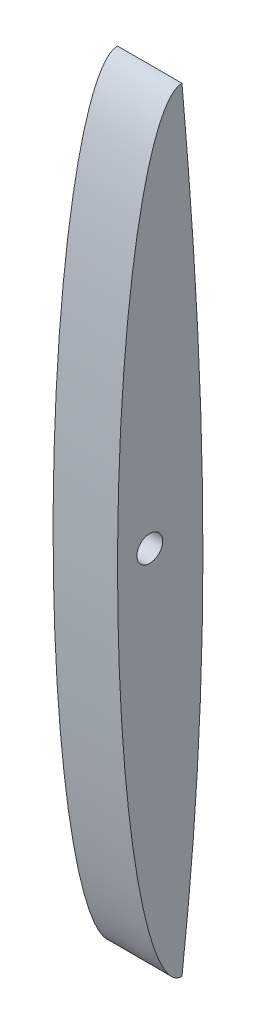
SolidWorks part; units mm, degrees
ref_plane "Front Plane" through (0, 0, 0) normal (0, 0, 1) x (1, 0, 0)
ref_plane "Top Plane" through (0, 0, 0) normal (0, 1, 0) x (1, 0, 0)
ref_plane "Right Plane" through (0, 0, 0) normal (1, 0, 0) x (0, 0, -1)
sketch "Sketch1" plane through (0, 0, 0) normal (1, 0, 0) x (0, 0, -1)
  line L0 (0, 0) -> (0, -60) construction
  line L1 (-5, -30) -> (0, -30) construction
  circle A0 centre (-2.5, -30) radius 1
  ellipse E0 centre (0, -30) end of major axis (0, -60) minor radius 5 (0, 0) -> (0, -60) ccw
  spline S0 degree 3 poles (0, 0) (0.0002, -0.0017) (0.0008, -0.0096) (0.002, -0.0231) (0.0035, -0.0401) (0.0049, -0.0559) (0.0061, -0.0705) (0.0074, -0.0844) (0.0085, -0.0975) (0.0096, -0.11) (0.0106, -0.122) (0.0116, -0.1334) (0.0125, -0.1439) (0.0134, -0.1535) (0.0141, -0.1621) (0.0148, -0.1698) (0.0154, -0.1766) (0.0159, -0.1825) (0.0163, -0.1873) (0.0166, -0.1911) (0.0169, -0.194) (0.0171, -0.1962) (0.0172, -0.1982) (0.0174, -0.2) (0.0176, -0.202) (0.0178, -0.2041) (0.0181, -0.208) (0.0186, -0.214) (0.0193, -0.2222) (0.0201, -0.2309) (0.0209, -0.2402) (0.0218, -0.2502) (0.0228, -0.2619) (0.0239, -0.2752) (0.0252, -0.2903) (0.0267, -0.3066) (0.0282, -0.3241) (0.0298, -0.3427) (0.0315, -0.3624) (0.0333, -0.3831) (0.0351, -0.4046) (0.037, -0.4265) (0.039, -0.4485) (0.0409, -0.4708) (0.0437, -0.5036) (0.0475, -0.5473) (0.0521, -0.6004) (0.0566, -0.6528) (0.0611, -0.7045) (0.0656, -0.7571) (0.0702, -0.8106) (0.0748, -0.8647) (0.0795, -0.9194) (0.0843, -0.9745) (0.0891, -1.0306) (0.094, -1.0879) (0.099, -1.1464) (0.1041, -1.2062) (0.1093, -1.2669) (0.1146, -1.3285) (0.1199, -1.3906) (0.1252, -1.4533) (0.1306, -1.5164) (0.136, -1.5804) (0.1416, -1.6458) (0.1472, -1.7124) (0.153, -1.7805) (0.1588, -1.8493) (0.1646, -1.9187) (0.1705, -1.9885) (0.1765, -2.0588) (0.1834, -2.1411) (0.1913, -2.2355) (0.2003, -2.3422) (0.2093, -2.4499) (0.2183, -2.5585) (0.2275, -2.668) (0.2365, -2.7763) (0.2453, -2.8834) (0.2541, -2.9893) (0.2629, -3.0959) (0.2718, -3.2034) (0.2807, -3.3118) (0.2896, -3.4209) (0.2987, -3.5309) (0.3077, -3.6418) (0.3168, -3.7534) (0.3246, -3.8489) (0.331, -3.928) (0.336, -3.9901) (0.341, -4.0518) (0.3456, -4.1082) (0.3497, -4.1595) (0.3534, -4.2056) (0.3571, -4.251) (0.3609, -4.2982) (0.3648, -4.3472) (0.3689, -4.3979) (0.3729, -4.4475) (0.3767, -4.4961) (0.3806, -4.5438) (0.3843, -4.5904) (0.3878, -4.6348) (0.3912, -4.677) (0.3944, -4.717) (0.3975, -4.7563) (0.4006, -4.7946) (0.4035, -4.8322) (0.406, -4.8627) (0.4078, -4.8863) (0.4092, -4.9033) (0.4105, -4.9195) (0.4117, -4.9349) (0.4128, -4.9494) (0.4139, -4.9629) (0.4149, -4.9758) (0.4159, -4.9881) (0.4168, -4.9997) (0.4177, -5.0101) (0.4184, -5.0194) (0.419, -5.0272) (0.4195, -5.0336) (0.4199, -5.0387) (0.4202, -5.043) (0.4205, -5.0467) (0.4208, -5.0502) (0.4212, -5.0544) (0.4215, -5.0594) (0.422, -5.0655) (0.4226, -5.0723) (0.4232, -5.0801) (0.4239, -5.0889) (0.4247, -5.0989) (0.4255, -5.1097) (0.4264, -5.1214) (0.4274, -5.1341) (0.4285, -5.1473) (0.4296, -5.1611) (0.4307, -5.1755) (0.4319, -5.1907) (0.4332, -5.2067) (0.4345, -5.2241) (0.436, -5.2432) (0.4377, -5.2638) (0.4394, -5.2855) (0.4411, -5.3081) (0.443, -5.3318) (0.4449, -5.3564) (0.4469, -5.382) (0.4491, -5.41) (0.4515, -5.4402) (0.454, -5.4724) (0.4566, -5.5048) (0.4591, -5.5373) (0.4616, -5.5697) (0.4641, -5.602) (0.4704, -5.6826) (0.4806, -5.8132) (0.4945, -5.9932) (0.5085, -6.1742) (0.5223, -6.3542) (0.5359, -6.5331) (0.5485, -6.6984) (0.56, -6.8503) (0.5704, -6.989) (0.5808, -7.1275) (0.5912, -7.266) (0.6079, -7.4895) (0.6307, -7.7982) (0.6507, -8.0715) (0.6618, -8.2243) (0.6642, -8.2567) (0.6665, -8.2891) (0.6689, -8.3214) (0.6712, -8.3535) (0.6736, -8.3868) (0.6761, -8.421) (0.6786, -8.4559) (0.681, -8.4897) (0.6834, -8.5226) (0.6857, -8.5545) (0.6879, -8.5855) (0.6901, -8.6152) (0.6921, -8.6438) (0.6941, -8.6712) (0.696, -8.6974) (0.6977, -8.7224) (0.6994, -8.7461) (0.7011, -8.7687) (0.7026, -8.7901) (0.704, -8.8103) (0.7052, -8.8273) (0.7062, -8.8413) (0.707, -8.8525) (0.7078, -8.8628) (0.7084, -8.8722) (0.709, -8.8804) (0.7095, -8.8873) (0.7099, -8.893) (0.7103, -8.8975) (0.7105, -8.9014) (0.7108, -8.9052) (0.7111, -8.9093) (0.7114, -8.9137) (0.7118, -8.9192) (0.7123, -8.926) (0.7129, -8.934) (0.7135, -8.9429) (0.7142, -8.953) (0.715, -8.9644) (0.7159, -8.9773) (0.7169, -8.9911) (0.718, -9.006) (0.7191, -9.0218) (0.7203, -9.0386) (0.7215, -9.0564) (0.7229, -9.0755) (0.7243, -9.0959) (0.7259, -9.1178) (0.7275, -9.1407) (0.7292, -9.1647) (0.731, -9.1898) (0.7328, -9.2151) (0.7346, -9.2406) (0.7364, -9.2662) (0.7382, -9.2927) (0.7402, -9.32) (0.7421, -9.3483) (0.7442, -9.3769) (0.7462, -9.4057) (0.7482, -9.4348) (0.7503, -9.4647) (0.7525, -9.4954) (0.7547, -9.5269) (0.7569, -9.5592) (0.7592, -9.5923) (0.7616, -9.6262) (0.764, -9.6608) (0.7688, -9.7302) (0.7771, -9.8501) (0.7889, -10.0202) (0.8016, -10.2057) (0.8145, -10.3947) (0.8275, -10.5871) (0.8407, -10.783) (0.8537, -10.9779) (0.8665, -11.1718) (0.8774, -11.3365) (0.8863, -11.4723) (0.8917, -11.555) (0.8955, -11.613) (0.8977, -11.6466) (0.8998, -11.68) (0.902, -11.7132) (0.9043, -11.7488) (0.9067, -11.7866) (0.9093, -11.8264) (0.9118, -11.8651) (0.9142, -11.9029) (0.9166, -11.9396) (0.9189, -11.9754) (0.9211, -12.0101) (0.9233, -12.0438) (0.9254, -12.0765) (0.9274, -12.1082) (0.9294, -12.1388) (0.9313, -12.1685) (0.9331, -12.1971) (0.9348, -12.224) (0.9364, -12.2492) (0.9379, -12.2728) (0.9393, -12.2955) (0.9407, -12.3174) (0.9421, -12.3384) (0.9432, -12.3567) (0.9442, -12.3724) (0.945, -12.3854) (0.9458, -12.3976) (0.9465, -12.4089) (0.9472, -12.4192) (0.9478, -12.4285) (0.9483, -12.4369) (0.9487, -12.4443) (0.9492, -12.4514) (0.9496, -12.4586) (0.9502, -12.468) (0.951, -12.48) (0.9519, -12.4946) (0.9529, -12.51) (0.9539, -12.5261) (0.955, -12.5438) (0.9562, -12.5631) (0.9575, -12.5839) (0.9589, -12.6058) (0.9603, -12.6287) (0.9618, -12.6525) (0.9634, -12.6773) (0.965, -12.7032) (0.9666, -12.7295) (0.9683, -12.7563) (0.97, -12.7836) (0.9718, -12.8118) (0.9736, -12.8409) (0.9754, -12.8708) (0.9773, -12.9011) (0.9792, -12.9316) (0.9811, -12.9623) (0.983, -12.9938) (0.985, -13.0261) (0.9871, -13.0592) (0.9892, -13.0931) (0.9913, -13.1278) (0.9935, -13.1632) (0.9957, -13.1995) (0.998, -13.2363) (1.0002, -13.2737) (1.0026, -13.3117) (1.0049, -13.3503) (1.0077, -13.3964) (1.011, -13.4502) (1.0147, -13.5118) (1.0185, -13.5746) (1.0223, -13.6385) (1.0263, -13.7036) (1.0301, -13.7685) (1.034, -13.8332) (1.0379, -13.8978) (1.0417, -13.9633) (1.0457, -14.0299) (1.0496, -14.0966) (1.0536, -14.1635) (1.0575, -14.2304) (1.0615, -14.2983) (1.0655, -14.3672) (1.0696, -14.437) (1.0736, -14.5064) (1.0776, -14.5753) (1.0815, -14.6437) (1.0855, -14.713) (1.0895, -14.7831) (1.0936, -14.8541) (1.0977, -14.9259) (1.1018, -14.9986) (1.1059, -15.0721) (1.1101, -15.1464) (1.1134, -15.2055) (1.1159, -15.2491) (1.1175, -15.277) (1.119, -15.305) (1.1206, -15.3329) (1.1221, -15.3604) (1.1237, -15.3886) (1.1253, -15.4174) (1.1269, -15.4466) (1.1285, -15.4746) (1.1299, -15.5008) (1.1313, -15.5253) (1.1325, -15.5481) (1.1337, -15.5699) (1.1349, -15.5906) (1.1359, -15.6104) (1.137, -15.6291) (1.1379, -15.6463) (1.1388, -15.6622) (1.1396, -15.6767) (1.1403, -15.6903) (1.141, -15.7031) (1.1417, -15.715) (1.1423, -15.7261) (1.1429, -15.7364) (1.1434, -15.7457) (1.1438, -15.7543) (1.1443, -15.7619) (1.1446, -15.7688) (1.1449, -15.7744) (1.1452, -15.7789) (1.1454, -15.7825) (1.1455, -15.7856) (1.1457, -15.7885) (1.1459, -15.7917) (1.1461, -15.7956) (1.1463, -15.8002) (1.1466, -15.8055) (1.147, -15.8115) (1.1473, -15.818) (1.1477, -15.8248) (1.1481, -15.8319) (1.1485, -15.8392) (1.149, -15.8497) (1.1498, -15.8635) (1.1507, -15.881) (1.1518, -15.9) (1.1529, -15.9205) (1.1541, -15.9426) (1.1553, -15.9657) (1.1567, -15.9901) (1.1581, -16.017) (1.1597, -16.0461) (1.1614, -16.0773) (1.163, -16.1088) (1.1648, -16.1406) (1.1665, -16.1725) (1.1682, -16.2048) (1.1704, -16.2464) (1.1731, -16.2976) (1.1764, -16.3585) (1.1797, -16.4218) (1.1832, -16.4875) (1.1868, -16.5555) (1.1904, -16.6245) (1.194, -16.6944) (1.1977, -16.7652) (1.2014, -16.837) (1.2052, -16.9098) (1.209, -16.9835) (1.2128, -17.0583) (1.2167, -17.1337) (1.2205, -17.2097) (1.2244, -17.2863) (1.2283, -17.3639) (1.2321, -17.4406) (1.2359, -17.5163) (1.2396, -17.5908) (1.2434, -17.6663) (1.2471, -17.7427) (1.2509, -17.8199) (1.2547, -17.8981) (1.2587, -17.9797) (1.2628, -18.0651) (1.2671, -18.154) (1.2714, -18.2441) (1.2758, -18.3352) (1.2793, -18.4087) (1.2819, -18.4643) (1.2836, -18.5017) (1.2854, -18.539) (1.2871, -18.5758) (1.2888, -18.6117) (1.2904, -18.6465) (1.2919, -18.6792) (1.2934, -18.7098) (1.2947, -18.7386) (1.296, -18.7663) (1.2972, -18.7931) (1.2984, -18.8188) (1.2995, -18.8436) (1.3006, -18.8674) (1.3017, -18.8902) (1.3027, -18.912) (1.3036, -18.9328) (1.3045, -18.9526) (1.3054, -18.9711) (1.3062, -18.9883) (1.3069, -19.0042) (1.3076, -19.0193) (1.3082, -19.0335) (1.3089, -19.0474) (1.3095, -19.061) (1.3101, -19.0741) (1.3106, -19.086) (1.3111, -19.0968) (1.3115, -19.1064) (1.3119, -19.1148) (1.3122, -19.1214) (1.3124, -19.1265) (1.3126, -19.1302) (1.3128, -19.1336) (1.3129, -19.1373) (1.3131, -19.1415) (1.3134, -19.1465) (1.3136, -19.1523) (1.3139, -19.1595) (1.3143, -19.1682) (1.3148, -19.1786) (1.3153, -19.19) (1.3159, -19.2023) (1.3165, -19.2157) (1.3171, -19.2297) (1.3178, -19.2443) (1.3184, -19.2596) (1.3192, -19.2757) (1.3199, -19.2927) (1.3207, -19.311) (1.3216, -19.3305) (1.3225, -19.3514) (1.3235, -19.3733) (1.3245, -19.3961) (1.3256, -19.4199) (1.3272, -19.4558) (1.3293, -19.5038) (1.3321, -19.5675) (1.3351, -19.6357) (1.3383, -19.7085) (1.3416, -19.7853) (1.3451, -19.8662) (1.3487, -19.9511) (1.3524, -20.0371) (1.3561, -20.1242) (1.3598, -20.2124) (1.3635, -20.3016) (1.3672, -20.3893) (1.3707, -20.4755) (1.3742, -20.5601) (1.3777, -20.6454) (1.3812, -20.7313) (1.3846, -20.8173) (1.391, -20.9767) (1.4002, -21.2094) (1.4119, -21.5152) (1.4231, -21.8142) (1.4307, -22.0218) (1.4349, -22.1382) (1.436, -22.1695) (1.4371, -22.2002) (1.4381, -22.2281) (1.439, -22.2528) (1.4398, -22.2747) (1.4406, -22.2958) (1.4413, -22.3171) (1.4421, -22.3385) (1.4428, -22.3598) (1.4435, -22.3802) (1.4442, -22.3996) (1.4449, -22.4181) (1.4455, -22.4356) (1.4461, -22.4522) (1.4466, -22.4681) (1.4471, -22.4832) (1.4476, -22.4975) (1.4481, -22.5107) (1.4485, -22.523) (1.4489, -22.5341) (1.4493, -22.5445) (1.4496, -22.5539) (1.4499, -22.5624) (1.4502, -22.5697) (1.4503, -22.5753) (1.4505, -22.5797) (1.4506, -22.5835) (1.4508, -22.5879) (1.451, -22.5928) (1.4512, -22.5988) (1.4514, -22.606) (1.4517, -22.6145) (1.452, -22.6237) (1.4524, -22.6336) (1.4527, -22.6442) (1.4531, -22.6555) (1.4536, -22.6682) (1.454, -22.6824) (1.4546, -22.6982) (1.4552, -22.7149) (1.4558, -22.7325) (1.4564, -22.7511) (1.457, -22.7702) (1.4577, -22.7897) (1.4584, -22.8098) (1.4591, -22.8307) (1.4598, -22.8524) (1.4606, -22.8762) (1.4615, -22.9021) (1.4624, -22.9302) (1.4634, -22.9595) (1.4644, -22.9899) (1.4654, -23.019) (1.4663, -23.0467) (1.4672, -23.0729) (1.4681, -23.0997) (1.469, -23.1271) (1.4702, -23.1661) (1.4719, -23.2161) (1.4738, -23.2767) (1.4758, -23.3365) (1.4778, -23.3992) (1.4799, -23.4645) (1.482, -23.5324) (1.4841, -23.5991) (1.4861, -23.6647) (1.4881, -23.729) (1.4901, -23.7921) (1.492, -23.8541) (1.4938, -23.9148) (1.4956, -23.9744) (1.4974, -24.0328) (1.4991, -24.0899) (1.5006, -24.142) (1.502, -24.1892) (1.5032, -24.2316) (1.5044, -24.2735) (1.5057, -24.3153) (1.5069, -24.3575) (1.5082, -24.4044) (1.5097, -24.456) (1.5113, -24.5125) (1.5129, -24.5701) (1.5146, -24.6287) (1.5162, -24.6883) (1.5179, -24.7478) (1.5195, -24.8071) (1.5211, -24.8662) (1.5227, -24.9262) (1.5243, -24.9872) (1.526, -25.049) (1.5276, -25.1118) (1.5293, -25.1755) (1.531, -25.2402) (1.5326, -25.3058) (1.5341, -25.3623) (1.5353, -25.4094) (1.5362, -25.4464) (1.5371, -25.4826) (1.538, -25.5181) (1.5389, -25.5526) (1.5397, -25.5864) (1.5405, -25.6209) (1.5414, -25.6562) (1.5423, -25.692) (1.5431, -25.7268) (1.5439, -25.7604) (1.5447, -25.7929) (1.5454, -25.8243) (1.5461, -25.8538) (1.5468, -25.8815) (1.5474, -25.9073) (1.548, -25.9323) (1.5486, -25.9563) (1.5491, -25.9794) (1.5495, -25.9984) (1.5499, -26.0137) (1.5502, -26.0254) (1.5504, -26.0367) (1.5507, -26.0474) (1.5509, -26.0573) (1.5511, -26.0668) (1.5513, -26.0759) (1.5515, -26.0844) (1.5517, -26.0918) (1.5518, -26.0976) (1.5519, -26.1022) (1.552, -26.106) (1.5521, -26.1097) (1.5522, -26.1138) (1.5523, -26.119) (1.5525, -26.1254) (1.5526, -26.1331) (1.5528, -26.1419) (1.5531, -26.1519) (1.5533, -26.1631) (1.5536, -26.1754) (1.5539, -26.1886) (1.5542, -26.2028) (1.5545, -26.2181) (1.5549, -26.2343) (1.5553, -26.2518) (1.5557, -26.2707) (1.5562, -26.291) (1.5566, -26.3123) (1.5571, -26.3348) (1.5577, -26.3583) (1.5582, -26.3817) (1.5587, -26.4049) (1.5592, -26.4277) (1.5597, -26.4512) (1.5602, -26.475) (1.5607, -26.499) (1.5612, -26.523) (1.5625, -26.5831) (1.5647, -26.6864) (1.5677, -26.833) (1.5708, -26.987) (1.5738, -27.1417) (1.5767, -27.2971) (1.5796, -27.4532) (1.5824, -27.61) (1.5851, -27.7674) (1.588, -27.9426) (1.5911, -28.135) (1.5942, -28.3442) (1.5973, -28.5526) (1.6001, -28.7601) (1.6028, -28.9667) (1.6046, -29.1136) (1.6056, -29.2011) (1.6059, -29.2294) (1.6063, -29.2575) (1.6066, -29.2851) (1.6069, -29.3118) (1.6072, -29.3371) (1.6074, -29.3609) (1.6077, -29.3834) (1.6079, -29.405) (1.6081, -29.4257) (1.6084, -29.4456) (1.6086, -29.4645) (1.6088, -29.4826) (1.6089, -29.4998) (1.6091, -29.5162) (1.6093, -29.5316) (1.6094, -29.546) (1.6096, -29.5595) (1.6097, -29.5721) (1.6098, -29.5839) (1.6099, -29.595) (1.61, -29.6053) (1.6101, -29.6146) (1.6102, -29.6231) (1.6103, -29.6307) (1.6104, -29.6374) (1.6104, -29.6434) (1.6105, -29.6487) (1.6105, -29.6536) (1.6106, -29.6585) (1.6106, -29.6639) (1.6107, -29.6701) (1.6108, -29.6772) (1.6108, -29.6853) (1.6109, -29.6942) (1.611, -29.7041) (1.6111, -29.7152) (1.6112, -29.7272) (1.6114, -29.7403) (1.6115, -29.7543) (1.6117, -29.7693) (1.6118, -29.7849) (1.612, -29.8011) (1.6121, -29.8178) (1.6123, -29.8355) (1.6125, -29.8539) (1.6126, -29.8733) (1.6128, -29.8935) (1.613, -29.9145) (1.6132, -29.9364) (1.6134, -29.9592) (1.6136, -29.9826) (1.6138, -30.0068) (1.614, -30.0316) (1.6143, -30.0573) (1.6145, -30.0866) (1.6148, -30.1193) (1.6151, -30.1552) (1.6154, -30.1913) (1.6157, -30.2274) (1.6159, -30.2635) (1.6162, -30.2996) (1.6169, -30.3898) (1.6184, -30.602) (1.6204, -30.9361) (1.6217, -31.2291) (1.6223, -31.4129) (1.6226, -31.4878) (1.6228, -31.5627) (1.623, -31.6376) (1.6232, -31.7124) (1.6233, -31.7816) (1.6234, -31.8447) (1.6235, -31.9017) (1.6236, -31.9578) (1.6236, -32.0129) (1.6237, -32.0672) (1.6237, -32.1207) (1.6238, -32.1732) (1.6238, -32.2249) (1.6238, -32.2756) (1.6238, -32.3255) (1.6238, -32.3745) (1.6237, -32.4218) (1.6237, -32.4672) (1.6237, -32.511) (1.6236, -32.554) (1.6236, -32.5962) (1.6235, -32.6356) (1.6235, -32.6722) (1.6234, -32.7061) (1.6234, -32.7349) (1.6233, -32.7589) (1.6233, -32.778) (1.6233, -32.7964) (1.6232, -32.8133) (1.6232, -32.8285) (1.6232, -32.8422) (1.6231, -32.8549) (1.6231, -32.8667) (1.6231, -32.8775) (1.6231, -32.8874) (1.623, -32.8964) (1.623, -32.9042) (1.623, -32.9109) (1.623, -32.9165) (1.623, -32.9214) (1.623, -32.9255) (1.623, -32.9292) (1.6229, -32.9331) (1.6229, -32.9377) (1.6229, -32.9433) (1.6229, -32.9499) (1.6229, -32.9576) (1.6229, -32.9663) (1.6228, -32.9761) (1.6228, -32.9867) (1.6228, -32.9981) (1.6227, -33.0099) (1.6227, -33.0253) (1.6226, -33.0445) (1.6226, -33.0679) (1.6225, -33.0922) (1.6224, -33.1176) (1.6223, -33.1438) (1.6222, -33.1708) (1.6221, -33.1987) (1.622, -33.2275) (1.6219, -33.2575) (1.6218, -33.2887) (1.6217, -33.3211) (1.6215, -33.3546) (1.6214, -33.389) (1.6212, -33.4245) (1.621, -33.461) (1.6209, -33.4984) (1.6207, -33.5369) (1.6205, -33.5763) (1.6203, -33.6165) (1.6201, -33.6571) (1.6198, -33.7105) (1.6194, -33.7764) (1.6189, -33.8518) (1.6185, -33.9236) (1.618, -33.9918) (1.6176, -34.0594) (1.617, -34.1305) (1.6165, -34.2049) (1.6159, -34.2826) (1.6153, -34.3594) (1.6146, -34.4351) (1.614, -34.5098) (1.6133, -34.5813) (1.6127, -34.6496) (1.6121, -34.7148) (1.6115, -34.7793) (1.6108, -34.8433) (1.6102, -34.9073) (1.6092, -35.0008) (1.6078, -35.124) (1.606, -35.2774) (1.6041, -35.4319) (1.6027, -35.5429) (1.6018, -35.6101) (1.6015, -35.6331) (1.6012, -35.6558) (1.6009, -35.678) (1.6006, -35.6993) (1.6003, -35.7192) (1.6001, -35.7378) (1.5998, -35.7552) (1.5996, -35.7716) (1.5994, -35.7872) (1.5992, -35.8026) (1.599, -35.8177) (1.5988, -35.8324) (1.5986, -35.846) (1.5984, -35.8583) (1.5982, -35.8695) (1.5981, -35.8795) (1.598, -35.8874) (1.5979, -35.8936) (1.5978, -35.8986) (1.5977, -35.9041) (1.5976, -35.9104) (1.5975, -35.9175) (1.5974, -35.9253) (1.5973, -35.9337) (1.5972, -35.9425) (1.597, -35.9545) (1.5968, -35.9696) (1.5965, -35.9883) (1.5962, -36.008) (1.5959, -36.0288) (1.5956, -36.049) (1.5953, -36.0684) (1.595, -36.0868) (1.5947, -36.1055) (1.5944, -36.1245) (1.594, -36.1521) (1.5934, -36.1886) (1.5927, -36.2344) (1.592, -36.2812) (1.5912, -36.3293) (1.5905, -36.3726) (1.5899, -36.4111) (1.5893, -36.4445) (1.5887, -36.4783) (1.5882, -36.5126) (1.5876, -36.5473) (1.587, -36.5829) (1.5863, -36.6188) (1.5857, -36.6548) (1.5851, -36.6899) (1.5845, -36.7239) (1.5839, -36.7569) (1.5833, -36.7886) (1.5828, -36.8193) (1.5822, -36.849) (1.5817, -36.8779) (1.5811, -36.9061) (1.5806, -36.9335) (1.5801, -36.9599) (1.5797, -36.9854) (1.5792, -37.0099) (1.5787, -37.0334) (1.5783, -37.0544) (1.578, -37.0735) (1.5776, -37.0912) (1.5773, -37.1095) (1.5769, -37.1285) (1.5765, -37.1481) (1.5761, -37.1682) (1.5757, -37.1889) (1.5753, -37.2103) (1.5748, -37.2339) (1.5743, -37.2597) (1.5737, -37.2878) (1.5732, -37.3169) (1.5725, -37.3469) (1.5719, -37.3779) (1.5712, -37.4109) (1.5705, -37.4459) (1.5697, -37.483) (1.5689, -37.5213) (1.5681, -37.5607) (1.5672, -37.6012) (1.5663, -37.6429) (1.5654, -37.6845) (1.5645, -37.7259) (1.5636, -37.7671) (1.5626, -37.8093) (1.5617, -37.8525) (1.5607, -37.8966) (1.5598, -37.9348) (1.5591, -37.9671) (1.5585, -37.993) (1.5579, -38.0193) (1.5572, -38.0458) (1.5566, -38.0723) (1.556, -38.1) (1.5553, -38.1285) (1.5546, -38.1576) (1.5539, -38.186) (1.5533, -38.2136) (1.5526, -38.2405) (1.552, -38.2666) (1.5514, -38.2919) (1.5508, -38.3162) (1.5502, -38.3396) (1.5496, -38.3621) (1.5491, -38.3834) (1.5486, -38.4035) (1.5481, -38.4225) (1.5477, -38.4406) (1.5472, -38.4579) (1.5468, -38.4744) (1.5464, -38.4908) (1.546, -38.5072) (1.5456, -38.5233) (1.5452, -38.5383) (1.5449, -38.5516) (1.5446, -38.5634) (1.5443, -38.5738) (1.5441, -38.5832) (1.5439, -38.5917) (1.5437, -38.5993) (1.5435, -38.6059) (1.5433, -38.6116) (1.5432, -38.6159) (1.5432, -38.619) (1.5431, -38.6213) (1.543, -38.6237) (1.543, -38.6266) (1.5429, -38.6302) (1.5427, -38.6347) (1.5426, -38.6401) (1.5424, -38.6464) (1.5423, -38.6536) (1.5421, -38.6612) (1.5419, -38.6692) (1.5416, -38.6791) (1.5413, -38.6911) (1.5409, -38.7053) (1.5405, -38.7203) (1.5401, -38.7362) (1.5397, -38.753) (1.5392, -38.7711) (1.5387, -38.7906) (1.5381, -38.8115) (1.5375, -38.8334) (1.5369, -38.8566) (1.5362, -38.8813) (1.5356, -38.9072) (1.5344, -38.948) (1.5329, -39.003) (1.5311, -39.0693) (1.5294, -39.1322) (1.5277, -39.1917) (1.526, -39.2504) (1.5245, -39.303) (1.5232, -39.3497) (1.522, -39.3907) (1.5208, -39.4311) (1.5197, -39.4712) (1.5185, -39.5107) (1.5173, -39.5499) (1.5161, -39.5905) (1.5148, -39.6332) (1.5135, -39.6781) (1.5121, -39.7242) (1.5107, -39.7714) (1.5092, -39.8196) (1.5076, -39.869) (1.5061, -39.9194) (1.5044, -39.971) (1.5028, -40.0236) (1.5011, -40.077) (1.4993, -40.1311) (1.4976, -40.186) (1.4958, -40.242) (1.4939, -40.2971) (1.4922, -40.3515) (1.4904, -40.405) (1.4886, -40.4593) (1.487, -40.5056) (1.4857, -40.5436) (1.4847, -40.5731) (1.4837, -40.6025) (1.4827, -40.6314) (1.4817, -40.6595) (1.4808, -40.6868) (1.4799, -40.7131) (1.479, -40.7386) (1.4782, -40.7631) (1.4773, -40.7868) (1.4765, -40.8096) (1.4758, -40.8312) (1.4751, -40.8514) (1.4744, -40.8705) (1.4737, -40.8888) (1.4731, -40.9063) (1.4725, -40.9233) (1.4719, -40.9398) (1.4714, -40.9558) (1.4708, -40.9709) (1.4703, -40.9851) (1.4698, -40.9984) (1.4694, -41.0106) (1.469, -41.0218) (1.4686, -41.0319) (1.4683, -41.0413) (1.468, -41.0498) (1.4677, -41.0572) (1.4675, -41.0635) (1.4673, -41.069) (1.4671, -41.0745) (1.4669, -41.0803) (1.4666, -41.0865) (1.4664, -41.0924) (1.4662, -41.0981) (1.466, -41.1038) (1.4658, -41.1104) (1.4655, -41.118) (1.4652, -41.1265) (1.4648, -41.136) (1.4645, -41.1468) (1.464, -41.1588) (1.4635, -41.172) (1.463, -41.1864) (1.4624, -41.2019) (1.4618, -41.2184) (1.4612, -41.2347) (1.4606, -41.2506) (1.4601, -41.2659) (1.4595, -41.2818) (1.4589, -41.2979) (1.4583, -41.314) (1.4572, -41.3438) (1.4556, -41.3869) (1.4534, -41.4432) (1.4513, -41.5001) (1.4491, -41.5575) (1.4469, -41.6154) (1.4447, -41.6725) (1.4425, -41.7288) (1.4402, -41.7864) (1.4379, -41.8452) (1.4355, -41.9052) (1.4332, -41.9641) (1.4308, -42.022) (1.4285, -42.0789) (1.4263, -42.1347) (1.424, -42.1896) (1.4218, -42.244) (1.4195, -42.2981) (1.4173, -42.3517) (1.4151, -42.4043) (1.4129, -42.4557) (1.4108, -42.506) (1.4087, -42.5553) (1.4067, -42.6022) (1.4048, -42.6467) (1.403, -42.689) (1.4012, -42.7303) (1.3994, -42.7707) (1.3977, -42.8102) (1.3961, -42.847) (1.3946, -42.881) (1.3932, -42.9123) (1.3919, -42.9427) (1.3906, -42.9722) (1.3893, -43.0009) (1.3881, -43.0286) (1.3868, -43.0564) (1.3856, -43.084) (1.3843, -43.1115) (1.3831, -43.1379) (1.382, -43.1632) (1.3809, -43.1868) (1.3799, -43.2087) (1.379, -43.2289) (1.3781, -43.2483) (1.3773, -43.2668) (1.3765, -43.2844) (1.3757, -43.3011) (1.375, -43.3175) (1.3742, -43.3333) (1.3735, -43.3486) (1.3729, -43.3629) (1.3723, -43.3761) (1.3717, -43.3882) (1.3712, -43.3993) (1.3707, -43.4093) (1.3703, -43.4182) (1.37, -43.4261) (1.3697, -43.4321) (1.3695, -43.4364) (1.3693, -43.4398) (1.3691, -43.4438) (1.3689, -43.4483) (1.3687, -43.4533) (1.3684, -43.4587) (1.3682, -43.4647) (1.3678, -43.4723) (1.3674, -43.4817) (1.3668, -43.4929) (1.3663, -43.5054) (1.3656, -43.5189) (1.3649, -43.5336) (1.3642, -43.5492) (1.3634, -43.5655) (1.3626, -43.5825) (1.3618, -43.6005) (1.3609, -43.6196) (1.36, -43.6385) (1.3591, -43.6571) (1.3583, -43.6751) (1.3574, -43.6934) (1.3565, -43.7117) (1.3557, -43.7299) (1.3544, -43.7562) (1.3528, -43.7905) (1.3503, -43.8414) (1.3475, -43.9003) (1.3442, -43.9672) (1.341, -44.0331) (1.3378, -44.0982) (1.3349, -44.1563) (1.3324, -44.2077) (1.3301, -44.2524) (1.3279, -44.2968) (1.3257, -44.3412) (1.3234, -44.3862) (1.3211, -44.4323) (1.3187, -44.478) (1.3164, -44.5235) (1.3141, -44.5685) (1.3117, -44.6145) (1.3093, -44.6614) (1.3068, -44.7092) (1.3042, -44.76) (1.3014, -44.8138) (1.2984, -44.8707) (1.2953, -44.9288) (1.2921, -44.988) (1.2889, -45.048) (1.2857, -45.1087) (1.2824, -45.1702) (1.279, -45.2329) (1.2762, -45.283) (1.2742, -45.3204) (1.2729, -45.3443) (1.2716, -45.3678) (1.2703, -45.3906) (1.2691, -45.4126) (1.2679, -45.4351) (1.2666, -45.4579) (1.2654, -45.481) (1.2641, -45.503) (1.263, -45.5241) (1.2618, -45.5443) (1.2608, -45.5635) (1.2598, -45.5816) (1.2588, -45.5987) (1.2579, -45.6147) (1.2571, -45.6295) (1.2563, -45.6433) (1.2556, -45.656) (1.2549, -45.6675) (1.2544, -45.678) (1.2538, -45.6874) (1.2534, -45.6957) (1.253, -45.7028) (1.2526, -45.7089) (1.2523, -45.7139) (1.2521, -45.7176) (1.252, -45.7202) (1.2519, -45.7224) (1.2517, -45.7251) (1.2515, -45.7285) (1.2513, -45.7327) (1.251, -45.7376) (1.2507, -45.7431) (1.2503, -45.749) (1.25, -45.7555) (1.2496, -45.7622) (1.2491, -45.7715) (1.2484, -45.7835) (1.2475, -45.7985) (1.2466, -45.8145) (1.2457, -45.8315) (1.2446, -45.8494) (1.2436, -45.868) (1.2425, -45.8871) (1.2414, -45.9067) (1.2402, -45.9272) (1.239, -45.9486) (1.2376, -45.9719) (1.2362, -45.9973) (1.2346, -46.0247) (1.2329, -46.0532) (1.2313, -46.0807) (1.2298, -46.1069) (1.2284, -46.1316) (1.2269, -46.1569) (1.2247, -46.194) (1.2219, -46.2425) (1.2184, -46.3021) (1.2148, -46.3623) (1.2112, -46.4232) (1.2075, -46.4846) (1.2039, -46.5452) (1.2003, -46.6049) (1.1967, -46.6638) (1.1932, -46.7218) (1.1897, -46.779) (1.1863, -46.8354) (1.1829, -46.8909) (1.1795, -46.9453) (1.1762, -46.9986) (1.1729, -47.0511) (1.1697, -47.1035) (1.1657, -47.1672) (1.1609, -47.2425) (1.1554, -47.3293) (1.1498, -47.417) (1.1444, -47.5019) (1.1391, -47.584) (1.1353, -47.6426) (1.1328, -47.6809) (1.1317, -47.6986) (1.1305, -47.7159) (1.1294, -47.7325) (1.1284, -47.7485) (1.1274, -47.7639) (1.1264, -47.7798) (1.1253, -47.7961) (1.1242, -47.8127) (1.1232, -47.8282) (1.1222, -47.8426) (1.1213, -47.856) (1.1205, -47.8682) (1.1198, -47.8791) (1.1192, -47.8888) (1.1186, -47.8971) (1.1181, -47.9046) (1.1177, -47.9114) (1.1173, -47.9177) (1.1169, -47.9234) (1.1165, -47.9287) (1.1162, -47.9342) (1.1158, -47.9402) (1.1153, -47.9468) (1.1149, -47.9541) (1.1143, -47.9627) (1.1136, -47.9726) (1.1129, -47.984) (1.1121, -47.9962) (1.1112, -48.0099) (1.1101, -48.0249) (1.109, -48.0415) (1.1079, -48.0591) (1.1066, -48.0779) (1.1053, -48.0978) (1.1039, -48.1183) (1.1025, -48.1396) (1.101, -48.1614) (1.0995, -48.1843) (1.0979, -48.2081) (1.0962, -48.2329) (1.0944, -48.2588) (1.0926, -48.2856) (1.0907, -48.3135) (1.0888, -48.3423) (1.0848, -48.4014) (1.0787, -48.4905) (1.0705, -48.6091) (1.0623, -48.7273) (1.0541, -48.8445) (1.0457, -48.9637) (1.0371, -49.0849) (1.0282, -49.208) (1.0194, -49.3299) (1.0107, -49.4507) (1.0019, -49.5703) (0.9953, -49.6593) (0.991, -49.7179) (0.9889, -49.7462) (0.9868, -49.7739) (0.9848, -49.8008) (0.9829, -49.827) (0.9809, -49.854) (0.9788, -49.8815) (0.9767, -49.9096) (0.9747, -49.9367) (0.9727, -49.963) (0.9708, -49.9884) (0.9689, -50.013) (0.9672, -50.0365) (0.9655, -50.059) (0.9638, -50.0804) (0.9623, -50.1008) (0.9608, -50.1201) (0.9594, -50.1383) (0.9581, -50.1555) (0.9569, -50.1717) (0.9558, -50.1868) (0.9547, -50.2008) (0.9537, -50.2138) (0.9528, -50.2257) (0.9519, -50.2367) (0.9512, -50.2458) (0.9507, -50.2534) (0.9502, -50.2599) (0.9496, -50.2668) (0.9491, -50.2745) (0.9484, -50.2828) (0.9477, -50.2925) (0.9468, -50.3036) (0.9459, -50.3162) (0.9448, -50.3297) (0.9438, -50.3435) (0.9427, -50.3573) (0.9416, -50.3711) (0.9405, -50.3853) (0.9394, -50.3997) (0.9383, -50.4142) (0.9367, -50.4354) (0.9345, -50.4634) (0.9311, -50.5077) (0.9269, -50.5619) (0.9219, -50.6255) (0.9169, -50.6895) (0.9118, -50.7538) (0.9067, -50.8191) (0.9014, -50.8855) (0.8961, -50.953) (0.8916, -51.0085) (0.8882, -51.052) (0.8857, -51.0833) (0.8831, -51.1153) (0.8805, -51.1481) (0.8777, -51.1817) (0.8748, -51.2182) (0.8716, -51.2577) (0.8682, -51.3003) (0.8646, -51.344) (0.8609, -51.389) (0.8572, -51.4354) (0.8532, -51.4832) (0.8492, -51.5322) (0.8451, -51.5822) (0.8409, -51.633) (0.8367, -51.6847) (0.8323, -51.7371) (0.8279, -51.7906) (0.8233, -51.8452) (0.8187, -51.9008) (0.8139, -51.9576) (0.809, -52.0154) (0.8047, -52.0668) (0.8009, -52.1116) (0.7977, -52.1491) (0.7946, -52.1863) (0.7915, -52.2225) (0.7885, -52.257) (0.7857, -52.2899) (0.7831, -52.3211) (0.7805, -52.3516) (0.7779, -52.3811) (0.7755, -52.4097) (0.7731, -52.4372) (0.7708, -52.4638) (0.7686, -52.4895) (0.7664, -52.5145) (0.7643, -52.5386) (0.7623, -52.5619) (0.7604, -52.5844) (0.7587, -52.6035) (0.7573, -52.6194) (0.7562, -52.6323) (0.7551, -52.6447) (0.7541, -52.6564) (0.7532, -52.6675) (0.7523, -52.6776) (0.7515, -52.6869) (0.7508, -52.695) (0.7501, -52.702) (0.7496, -52.7079) (0.7492, -52.7124) (0.749, -52.7156) (0.7487, -52.7181) (0.7485, -52.7206) (0.7483, -52.7234) (0.748, -52.7266) (0.7476, -52.731) (0.7471, -52.7367) (0.7465, -52.7441) (0.7457, -52.7524) (0.7449, -52.7617) (0.744, -52.772) (0.743, -52.7833) (0.742, -52.7956) (0.7408, -52.8089) (0.7395, -52.8231) (0.7382, -52.8383) (0.7368, -52.8545) (0.7354, -52.8703) (0.734, -52.8857) (0.7328, -52.9003) (0.7314, -52.9152) (0.7301, -52.9302) (0.7253, -52.9847) (0.7174, -53.0742) (0.7063, -53.1987) (0.6945, -53.33) (0.6816, -53.4727) (0.6704, -53.5957) (0.662, -53.6877) (0.6564, -53.749) (0.6507, -53.8107) (0.6446, -53.8772) (0.638, -53.9484) (0.631, -54.0245) (0.6238, -54.1015) (0.6165, -54.1794) (0.6091, -54.2583) (0.6014, -54.34) (0.5934, -54.4245) (0.5851, -54.5119) (0.5767, -54.6003) (0.5685, -54.6862) (0.5605, -54.7694) (0.5543, -54.8334) (0.5497, -54.8815) (0.5466, -54.9131) (0.5436, -54.9444) (0.5403, -54.9779) (0.5369, -55.0137) (0.5332, -55.0514) (0.5296, -55.0881) (0.5261, -55.1238) (0.5228, -55.1583) (0.5195, -55.1918) (0.5164, -55.2234) (0.5135, -55.2531) (0.5107, -55.281) (0.5081, -55.3081) (0.5055, -55.3342) (0.503, -55.3594) (0.5006, -55.3842) (0.4981, -55.4087) (0.4958, -55.4327) (0.4935, -55.4556) (0.4916, -55.4743) (0.4902, -55.4889) (0.4891, -55.4997) (0.4881, -55.5102) (0.4871, -55.5203) (0.4861, -55.5296) (0.4853, -55.5381) (0.4845, -55.5457) (0.4839, -55.5525) (0.4833, -55.5583) (0.4828, -55.5634) (0.4824, -55.5675) (0.482, -55.5712) (0.4816, -55.5752) (0.4811, -55.5799) (0.4806, -55.5855) (0.4799, -55.5921) (0.4792, -55.5997) (0.4783, -55.6082) (0.4774, -55.6177) (0.4763, -55.628) (0.4752, -55.6393) (0.474, -55.6514) (0.4727, -55.6643) (0.4713, -55.6781) (0.4699, -55.6929) (0.4683, -55.7088) (0.4666, -55.7255) (0.4649, -55.7426) (0.4631, -55.76) (0.4614, -55.7775) (0.4596, -55.7952) (0.4567, -55.8236) (0.4528, -55.8629) (0.4477, -55.9135) (0.4424, -55.9652) (0.4371, -56.018) (0.4316, -56.072) (0.4261, -56.1259) (0.4206, -56.1799) (0.4151, -56.2337) (0.4095, -56.2886) (0.4037, -56.3445) (0.3979, -56.4013) (0.3919, -56.4592) (0.3858, -56.518) (0.3796, -56.5778) (0.3733, -56.6385) (0.3669, -56.6999) (0.3605, -56.7617) (0.354, -56.8236) (0.3475, -56.8855) (0.3313, -57.0387) (0.3054, -57.2833) (0.2693, -57.6193) (0.2318, -57.9633) (0.2051, -58.206) (0.1894, -58.3471) (0.1859, -58.3787) (0.1824, -58.4101) (0.1789, -58.441) (0.1756, -58.4708) (0.1724, -58.4997) (0.1693, -58.5275) (0.1662, -58.5546) (0.1633, -58.5809) (0.1604, -58.6066) (0.1576, -58.6316) (0.1549, -58.6557) (0.1523, -58.679) (0.1497, -58.7013) (0.1473, -58.7226) (0.145, -58.743) (0.1428, -58.7625) (0.1406, -58.7824) (0.1383, -58.8024) (0.1361, -58.8224) (0.1339, -58.8413) (0.1319, -58.859) (0.13, -58.8756) (0.1285, -58.8892) (0.1273, -58.9002) (0.1263, -58.9087) (0.1254, -58.9168) (0.1245, -58.9244) (0.1237, -58.9315) (0.1229, -58.9382) (0.1223, -58.9441) (0.1217, -58.9492) (0.1212, -58.9532) (0.1209, -58.9559) (0.1207, -58.9578) (0.1205, -58.9593) (0.1203, -58.9613) (0.12, -58.9644) (0.1195, -58.9686) (0.1189, -58.9742) (0.1181, -58.9809) (0.1172, -58.9885) (0.1162, -58.9971) (0.1152, -59.0066) (0.114, -59.0172) (0.1126, -59.0287) (0.1112, -59.0413) (0.1097, -59.0549) (0.108, -59.0691) (0.1064, -59.0837) (0.1046, -59.0989) (0.1028, -59.1149) (0.1009, -59.1318) (0.0988, -59.1495) (0.0967, -59.1685) (0.0943, -59.1888) (0.0919, -59.2105) (0.0893, -59.2331) (0.0865, -59.2567) (0.0837, -59.2813) (0.0808, -59.3063) (0.0779, -59.3318) (0.0749, -59.3577) (0.0718, -59.3844) (0.0687, -59.4119) (0.0654, -59.4404) (0.062, -59.4696) (0.0585, -59.4998) (0.0549, -59.5308) (0.0512, -59.5627) (0.0474, -59.5952) (0.0435, -59.6284) (0.0396, -59.6622) (0.0356, -59.6969) (0.0314, -59.7326) (0.0271, -59.7694) (0.0227, -59.8072) (0.0181, -59.846) (0.0135, -59.8855) (0.0088, -59.9257) (0.0042, -59.964) (0.0013, -59.9887) (0, -60) knots 0 0 0 0 0.000087 0.000391 0.000679 0.000937 0.001181 0.001413 0.001631 0.001835 0.002041 0.002231 0.002406 0.002565 0.002709 0.002838 0.002951 0.003049 0.003132 0.003192 0.00324 0.003276 0.003306 0.003337 0.00337 0.003404 0.00344 0.003565 0.003707 0.003848 0.004002 0.00417 0.004351 0.004585 0.004838 0.005109 0.0054 0.00571 0.006039 0.006387 0.006749 0.007114 0.007482 0.007853 0.008228 0.009124 0.010039 0.010886 0.011749 0.012626 0.013519 0.014426 0.015333 0.016253 0.017189 0.018139 0.019121 0.020118 0.021131 0.022158 0.023201 0.02424 0.025293 0.026361 0.027443 0.028563 0.029697 0.030847 0.032005 0.033171 0.034343 0.035523 0.037287 0.039068 0.040863 0.042675 0.044502 0.046344 0.048096 0.049861 0.05164 0.053433 0.05524 0.057061 0.058896 0.060744 0.062607 0.064483 0.06552 0.066562 0.067594 0.068606 0.069387 0.070156 0.070913 0.071658 0.072519 0.073364 0.074192 0.075004 0.075798 0.076575 0.077336 0.078018 0.078687 0.079341 0.079981 0.080606 0.081218 0.081506 0.081791 0.082064 0.082321 0.082562 0.082788 0.082997 0.083209 0.083402 0.083576 0.083731 0.083867 0.083965 0.08405 0.084122 0.084181 0.084236 0.0843 0.084388 0.084488 0.084602 0.084728 0.084879 0.085045 0.085225 0.085421 0.085632 0.085857 0.086084 0.086324 0.086577 0.086843 0.087123 0.087451 0.087795 0.088156 0.088534 0.088928 0.089339 0.089766 0.09021 0.090738 0.091279 0.09182 0.092361 0.092901 0.09344 0.093979 0.096934 0.09997 0.102988 0.105989 0.108973 0.11194 0.114258 0.116568 0.118877 0.121187 0.123498 0.130059 0.136626 0.137166 0.137705 0.138245 0.138785 0.139323 0.139848 0.14045 0.141033 0.141596 0.142141 0.142677 0.143193 0.143689 0.144165 0.144622 0.145058 0.145475 0.145871 0.146247 0.146604 0.14694 0.147257 0.147454 0.147642 0.147816 0.147972 0.148109 0.148229 0.148317 0.148393 0.148454 0.148515 0.148582 0.148656 0.148736 0.148858 0.148993 0.149141 0.149301 0.149499 0.149713 0.149943 0.150191 0.150454 0.150735 0.151031 0.151344 0.15169 0.152054 0.152436 0.152837 0.153255 0.153691 0.154103 0.154529 0.154971 0.155427 0.155898 0.156384 0.156856 0.157341 0.15784 0.158352 0.158877 0.159415 0.159966 0.160531 0.161109 0.161696 0.164002 0.167108 0.1702 0.173277 0.176559 0.179823 0.183071 0.186303 0.189518 0.191308 0.193092 0.193651 0.194211 0.194769 0.195324 0.195869 0.196549 0.197212 0.197859 0.198488 0.1991 0.199696 0.200274 0.200836 0.201381 0.201909 0.20242 0.202914 0.203391 0.203851 0.204258 0.204651 0.205029 0.205394 0.205744 0.20608 0.206311 0.206528 0.206731 0.206919 0.207092 0.20725 0.207385 0.207507 0.207622 0.207741 0.207864 0.208094 0.208338 0.208594 0.208864 0.209147 0.209478 0.209826 0.21019 0.210571 0.210968 0.211382 0.211812 0.212259 0.212699 0.213154 0.213623 0.214108 0.214607 0.215121 0.21562 0.216132 0.216657 0.217195 0.217746 0.218311 0.218889 0.21948 0.220084 0.220702 0.221321 0.221953 0.222598 0.223252 0.224259 0.225286 0.226332 0.227396 0.228481 0.229584 0.230642 0.231717 0.232809 0.233918 0.235044 0.236144 0.23726 0.238391 0.239538 0.240701 0.24188 0.243006 0.244146 0.2453 0.246468 0.24765 0.248846 0.250057 0.251281 0.252519 0.253772 0.254234 0.254699 0.255166 0.255634 0.256093 0.256538 0.257044 0.257531 0.257998 0.258445 0.258841 0.259221 0.259583 0.259929 0.260258 0.26057 0.260865 0.26112 0.261362 0.261589 0.261802 0.262001 0.262185 0.262356 0.262512 0.262654 0.262782 0.262895 0.262995 0.263063 0.263123 0.263173 0.263216 0.263268 0.263334 0.26341 0.263498 0.263599 0.263709 0.263823 0.263941 0.264063 0.264188 0.264464 0.264755 0.265063 0.265412 0.265779 0.266165 0.266571 0.266995 0.267508 0.268029 0.268553 0.269082 0.269615 0.270151 0.270692 0.271694 0.272709 0.273738 0.274856 0.275989 0.277138 0.278302 0.279482 0.280677 0.281888 0.283116 0.284362 0.285625 0.286884 0.288159 0.289451 0.290761 0.291989 0.293231 0.294488 0.295759 0.297045 0.298346 0.299662 0.301126 0.302607 0.304107 0.305624 0.307159 0.307778 0.3084 0.309025 0.309642 0.310241 0.310819 0.311378 0.311873 0.312351 0.312813 0.313258 0.313687 0.3141 0.314495 0.314875 0.315238 0.315584 0.315914 0.316227 0.316507 0.316773 0.317024 0.31726 0.317482 0.31772 0.317938 0.318137 0.318316 0.318475 0.318615 0.318735 0.318806 0.318868 0.318921 0.318979 0.31905 0.319133 0.31923 0.319337 0.319493 0.319666 0.319855 0.320061 0.320283 0.320521 0.320761 0.321015 0.321283 0.321566 0.321863 0.322195 0.322542 0.322906 0.323286 0.323683 0.324095 0.325081 0.326077 0.327276 0.328488 0.329715 0.331111 0.332525 0.333957 0.335406 0.336873 0.338358 0.33986 0.341253 0.342661 0.344084 0.345516 0.346947 0.348377 0.353478 0.358566 0.363642 0.368406 0.36893 0.369453 0.369969 0.370466 0.370842 0.371206 0.371558 0.371897 0.372268 0.372623 0.372962 0.373286 0.373593 0.373885 0.374161 0.374421 0.374677 0.374915 0.375135 0.375339 0.375525 0.375693 0.375855 0.375996 0.376117 0.376219 0.376275 0.376338 0.37641 0.376491 0.376582 0.37671 0.376852 0.377006 0.377171 0.377347 0.377535 0.377734 0.377981 0.378243 0.378521 0.378814 0.379123 0.379447 0.379767 0.380101 0.380449 0.38081 0.381185 0.381635 0.382104 0.38259 0.383095 0.383619 0.384043 0.384479 0.384926 0.385384 0.385847 0.38687 0.387879 0.388874 0.389856 0.391005 0.392135 0.393245 0.394335 0.395406 0.396456 0.397487 0.398498 0.399488 0.400459 0.401411 0.402342 0.40306 0.403765 0.404458 0.40515 0.405852 0.406565 0.407488 0.408428 0.409386 0.410361 0.411353 0.412362 0.41333 0.414313 0.415311 0.416325 0.417354 0.418399 0.419459 0.420534 0.421625 0.422731 0.423357 0.423974 0.424577 0.425166 0.425741 0.426302 0.42685 0.427465 0.428061 0.428639 0.429198 0.429739 0.430262 0.430766 0.431212 0.431642 0.432057 0.432456 0.43284 0.433208 0.433407 0.433602 0.433791 0.43397 0.434135 0.434286 0.434447 0.434588 0.43471 0.434813 0.434882 0.434939 0.435 0.435069 0.435146 0.435259 0.435387 0.435529 0.435699 0.435885 0.436089 0.436309 0.436546 0.436799 0.437069 0.437356 0.437674 0.438011 0.438366 0.438739 0.439131 0.439541 0.439907 0.440286 0.440679 0.441078 0.441477 0.441876 0.442275 0.444477 0.447027 0.449588 0.452161 0.454746 0.457342 0.45995 0.46257 0.465198 0.468692 0.472172 0.475637 0.479088 0.482525 0.485948 0.486419 0.48689 0.48736 0.487821 0.488265 0.488693 0.489082 0.489455 0.489815 0.490159 0.490489 0.490805 0.491106 0.491392 0.491663 0.491921 0.492159 0.492383 0.492593 0.492789 0.492974 0.493145 0.493301 0.493442 0.493569 0.493679 0.493777 0.493866 0.493945 0.494021 0.49411 0.494214 0.494332 0.494466 0.494614 0.494777 0.494962 0.495163 0.49538 0.495613 0.495862 0.496128 0.496392 0.496671 0.496964 0.497271 0.497593 0.497929 0.498279 0.498643 0.499021 0.499414 0.499813 0.500227 0.500654 0.501094 0.501687 0.502287 0.502888 0.503488 0.504088 0.504688 0.505289 0.508588 0.515277 0.521958 0.523205 0.524451 0.525696 0.526942 0.528187 0.529429 0.530391 0.531338 0.532271 0.533189 0.534092 0.53498 0.535854 0.536713 0.537558 0.538387 0.539202 0.540003 0.540744 0.541472 0.542187 0.542889 0.543578 0.544151 0.544715 0.545269 0.545592 0.545911 0.546221 0.546511 0.546754 0.546981 0.547193 0.547389 0.547569 0.547734 0.547883 0.548016 0.548122 0.548216 0.548297 0.548365 0.548421 0.548482 0.548559 0.548652 0.548761 0.548889 0.549035 0.549197 0.549377 0.549567 0.549763 0.549964 0.550336 0.550724 0.551129 0.551551 0.551989 0.552437 0.5529 0.553379 0.553875 0.554398 0.554937 0.555493 0.556066 0.556656 0.557263 0.557886 0.558525 0.559181 0.559854 0.560532 0.561206 0.56252 0.56382 0.564967 0.566103 0.567228 0.56834 0.56965 0.570942 0.572219 0.573478 0.574722 0.575948 0.577046 0.578131 0.579202 0.580264 0.581329 0.582397 0.584928 0.58748 0.59005 0.592641 0.593022 0.593404 0.593786 0.594157 0.594511 0.594849 0.595152 0.595441 0.595714 0.595974 0.596218 0.596483 0.596728 0.596953 0.597159 0.597345 0.597512 0.597659 0.597739 0.597818 0.59791 0.598015 0.598133 0.598262 0.598404 0.598552 0.598706 0.598998 0.599309 0.599637 0.599983 0.600346 0.600644 0.600952 0.601265 0.601581 0.601901 0.602643 0.603404 0.604184 0.604983 0.605802 0.606349 0.606903 0.607467 0.608038 0.608618 0.609198 0.609813 0.610412 0.610996 0.611563 0.612114 0.612639 0.613149 0.613643 0.614122 0.614594 0.61505 0.61549 0.615914 0.616321 0.616712 0.617087 0.617372 0.617665 0.617969 0.618286 0.618614 0.618947 0.619292 0.619648 0.620016 0.620468 0.620936 0.62142 0.62192 0.622436 0.622968 0.623567 0.624184 0.624821 0.625477 0.626152 0.626845 0.627558 0.628228 0.628914 0.629617 0.630335 0.631069 0.631819 0.632246 0.632678 0.633115 0.633557 0.634002 0.634439 0.634939 0.635425 0.635897 0.636353 0.636804 0.637239 0.63766 0.638064 0.638454 0.638828 0.639187 0.639518 0.639834 0.640136 0.640424 0.640698 0.640957 0.641245 0.641514 0.641763 0.641992 0.64218 0.642353 0.64251 0.642651 0.642777 0.642887 0.642982 0.643061 0.643103 0.643139 0.643175 0.643222 0.643283 0.643357 0.643443 0.643554 0.643674 0.643801 0.643935 0.644075 0.644296 0.644532 0.644782 0.645047 0.645327 0.645621 0.645952 0.646299 0.646664 0.647045 0.647462 0.647897 0.648336 0.6495 0.650644 0.65165 0.652642 0.653618 0.65458 0.65527 0.655952 0.656626 0.657292 0.657951 0.658601 0.65925 0.659981 0.66073 0.661497 0.662283 0.663086 0.663908 0.664748 0.665607 0.666483 0.667378 0.668275 0.669189 0.670121 0.67107 0.671946 0.672837 0.673742 0.674662 0.67515 0.675641 0.676135 0.676618 0.677086 0.67754 0.677979 0.678403 0.678812 0.679207 0.679586 0.679951 0.680282 0.6806 0.680904 0.681196 0.681474 0.681755 0.682021 0.682272 0.682509 0.682731 0.682938 0.68312 0.683288 0.683444 0.683587 0.683716 0.683814 0.683903 0.683991 0.684088 0.684192 0.684303 0.684383 0.684476 0.684586 0.684712 0.684855 0.685013 0.685188 0.685391 0.685612 0.685852 0.68611 0.686386 0.68668 0.686924 0.687179 0.687446 0.687716 0.687985 0.688253 0.689202 0.69014 0.691066 0.692045 0.693011 0.693962 0.694901 0.695825 0.696841 0.69784 0.698821 0.699786 0.700734 0.701665 0.702579 0.703476 0.704388 0.705282 0.706157 0.707015 0.707854 0.708674 0.709477 0.710197 0.710901 0.71159 0.712264 0.712922 0.713565 0.714101 0.714622 0.715129 0.715621 0.716099 0.716561 0.717009 0.717485 0.717943 0.718383 0.718806 0.71921 0.719562 0.7199 0.720223 0.720531 0.720824 0.721103 0.721367 0.721641 0.721896 0.722134 0.722354 0.722556 0.722741 0.722907 0.723056 0.723187 0.7233 0.723355 0.723405 0.723469 0.723552 0.723631 0.723721 0.723821 0.723932 0.724101 0.724289 0.724496 0.724722 0.724968 0.725232 0.725499 0.725783 0.726084 0.726401 0.726736 0.727028 0.727331 0.727637 0.727942 0.728246 0.728549 0.729258 0.729962 0.731092 0.732207 0.733306 0.734391 0.73546 0.736214 0.73696 0.737699 0.738433 0.739182 0.73995 0.740736 0.741472 0.742223 0.74299 0.743772 0.744569 0.745382 0.746311 0.74726 0.748229 0.749216 0.750223 0.75123 0.752256 0.753301 0.754364 0.754766 0.755168 0.755561 0.755941 0.756309 0.756664 0.757066 0.757451 0.757818 0.758168 0.758507 0.758828 0.75913 0.759415 0.759681 0.759929 0.760158 0.76037 0.760563 0.760737 0.760894 0.761033 0.761151 0.761252 0.761336 0.761402 0.761436 0.761469 0.761513 0.76157 0.76164 0.761723 0.761813 0.761914 0.762022 0.762134 0.762251 0.762485 0.762736 0.763002 0.763286 0.763585 0.763901 0.764214 0.764542 0.764884 0.765241 0.765612 0.766051 0.766508 0.766984 0.767479 0.767881 0.768295 0.76872 0.769146 0.770152 0.771146 0.772128 0.773167 0.774191 0.775202 0.776198 0.777181 0.778149 0.779104 0.780044 0.780971 0.781883 0.782766 0.783637 0.784512 0.785391 0.786827 0.788277 0.78974 0.791217 0.792528 0.79385 0.794148 0.794446 0.794735 0.795013 0.795281 0.795536 0.795781 0.796076 0.796353 0.796612 0.796853 0.797076 0.79728 0.797467 0.797622 0.797762 0.797886 0.797998 0.798102 0.798197 0.798284 0.798372 0.798471 0.798582 0.798704 0.798838 0.799011 0.7992 0.799405 0.799626 0.799883 0.800159 0.800453 0.800767 0.801099 0.801449 0.801797 0.802162 0.802543 0.802941 0.803356 0.803787 0.804235 0.8047 0.805181 0.805679 0.807656 0.809645 0.811618 0.813573 0.815512 0.817587 0.819643 0.821679 0.823695 0.825692 0.827669 0.828152 0.828626 0.829088 0.829537 0.829975 0.830401 0.830887 0.831356 0.831808 0.832244 0.832672 0.833082 0.833474 0.833849 0.834207 0.834547 0.83487 0.835174 0.835462 0.835732 0.835984 0.836219 0.836433 0.836632 0.836816 0.836985 0.837091 0.837195 0.837311 0.837438 0.837578 0.837729 0.837922 0.838132 0.838359 0.838602 0.838821 0.839052 0.839291 0.839532 0.839774 0.840017 0.840595 0.841178 0.842235 0.843311 0.844366 0.845439 0.84653 0.847639 0.848766 0.84991 0.85042 0.850943 0.851478 0.852026 0.852587 0.853161 0.853854 0.854566 0.855295 0.856042 0.856822 0.85762 0.858437 0.859273 0.860127 0.860984 0.86186 0.862753 0.863665 0.864594 0.865542 0.866508 0.867491 0.868119 0.868752 0.869373 0.869978 0.870567 0.871104 0.871626 0.872133 0.872627 0.873107 0.873564 0.874008 0.874438 0.874854 0.875257 0.875646 0.876022 0.876384 0.876604 0.87682 0.877029 0.877227 0.877408 0.877582 0.877737 0.877872 0.877989 0.878087 0.878166 0.878214 0.878252 0.878291 0.878337 0.878391 0.878451 0.878557 0.87868 0.878819 0.878975 0.879147 0.879336 0.879541 0.879762 0.879999 0.880253 0.880524 0.880811 0.881048 0.881294 0.881544 0.881793 0.882043 0.884276 0.886277 0.888286 0.890852 0.893431 0.894447 0.895468 0.8965 0.897543 0.898798 0.90007 0.901357 0.902659 0.903977 0.90531 0.906753 0.908213 0.909692 0.911188 0.912519 0.913864 0.914396 0.914928 0.91545 0.915962 0.916611 0.917242 0.917856 0.918451 0.919029 0.919589 0.920131 0.920613 0.921079 0.92153 0.921967 0.922388 0.922795 0.923213 0.923614 0.923998 0.924365 0.92455 0.924731 0.924907 0.925077 0.925234 0.925376 0.925503 0.925616 0.925714 0.925797 0.925866 0.925921 0.925985 0.926064 0.926159 0.926268 0.926395 0.926537 0.926695 0.926869 0.927058 0.927259 0.927475 0.927706 0.927952 0.928218 0.9285 0.928788 0.929079 0.929372 0.929668 0.929966 0.930793 0.931639 0.932503 0.933386 0.934288 0.935208 0.936092 0.936993 0.93791 0.938844 0.939795 0.940761 0.941745 0.942744 0.943761 0.944793 0.945823 0.946859 0.947896 0.948932 0.954544 0.960163 0.965788 0.971809 0.97234 0.97287 0.973399 0.973915 0.974418 0.974898 0.975363 0.975816 0.976254 0.976686 0.977104 0.977508 0.977897 0.978273 0.978627 0.978968 0.979295 0.979608 0.979964 0.980299 0.980615 0.980912 0.981189 0.981447 0.981597 0.981739 0.981874 0.982001 0.982121 0.982234 0.982335 0.98242 0.982488 0.982536 0.982557 0.98258 0.982613 0.982659 0.982733 0.982826 0.982938 0.983068 0.98321 0.983369 0.983546 0.983739 0.983949 0.984177 0.984421 0.984661 0.984914 0.985182 0.985464 0.98576 0.986071 0.986418 0.98678 0.987159 0.987554 0.987966 0.988393 0.988812 0.989244 0.989691 0.990152 0.990628 0.991118 0.991623 0.992142 0.992676 0.993224 0.993776 0.994342 0.994922 0.995516 0.996135 0.996769 0.997417 0.998079 0.998756 0.999435 1 1 1 1
  dimension "D1" = 60
  dimension "D2" = 10
extrude "Boss-Extrude1" add sketch "Sketch1" along normal blind 5
